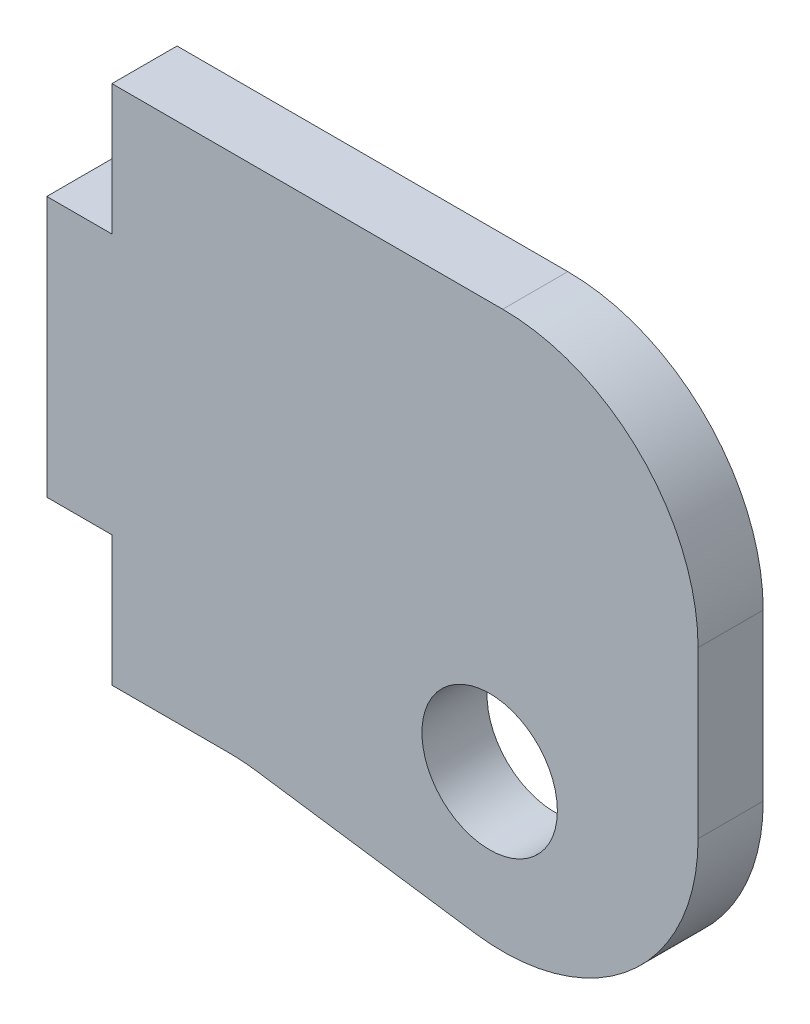
SolidWorks part; units mm, degrees
material "AISI 4340 Steel, normalized"
ref_plane "X-Y Datum" through (0, 0, 0) normal (0, 0, 1) x (1, 0, 0)
ref_plane "X-Z Datum" through (0, 0, 0) normal (0, 1, 0) x (1, 0, 0)
ref_plane "Y-Z Datum" through (0, 0, 0) normal (1, 0, 0) x (0, 0, -1)
sketch "Sketch1" plane through (0, 0, 0) normal (0, 0, 1) x (1, 0, 0)
  line L0 (0, 12.7) -> (0, -12.7)
  line L7 (31.75, -15.875) -> (31.75, 12.7)
  line L8 (31.75, 12.7) -> (0, 12.7)
  line L9 (0, -12.7) -> (9.525, -12.7)
  line L10 (9.525, -12.7) -> (31.75, -15.875)
  point P2 (0, 0)
  point P6 (0, 0)
  dimension "D1" = 25.4
  dimension "D2" = 31.75
  dimension "D3" = 28.575
  dimension "D4" = 9.525
extrude "Boss-Extrude1" add sketch "Sketch1" along normal blind 3.175
sketch "Sketch2" plane through (0, 0, 3.175) normal (0, 0, 1) x (1, 0, 0)
  circle A0 centre (21.5883, -7.1409) radius 3.302
  point P2 (0, 0)
  dimension "D1" = 6.604
extrude "Cut-Extrude1" cut sketch "Sketch2" against normal blind 3.175
fillet "Fillet1" radius 9.525 3 edges at (31.75, 12.7, 1.5875) (9.525, -12.7, 1.5875) (31.75, -15.875, 1.5875)
sketch "Sketch3" plane through (0, 0, 3.175) normal (0, 0, 1) x (1, 0, 0)
  line L1 (0, -12.7) -> (3.175, -12.7)
  line L2 (0, -12.7) -> (0, -6.35)
  line L3 (0, -6.35) -> (3.175, -6.35)
  line L4 (3.175, -12.7) -> (3.175, -6.35)
  line L5 (0, 12.7) -> (3.175, 12.7)
  line L6 (0, 12.7) -> (0, 6.35)
  line L7 (0, 6.35) -> (3.175, 6.35)
  line L8 (3.175, 12.7) -> (3.175, 6.35)
  point P9 (0, 0)
  dimension "D1" = 3.175
  dimension "D2" = 12.7
extrude "Cut-Extrude2" cut sketch "Sketch3" against normal blind 3.175
